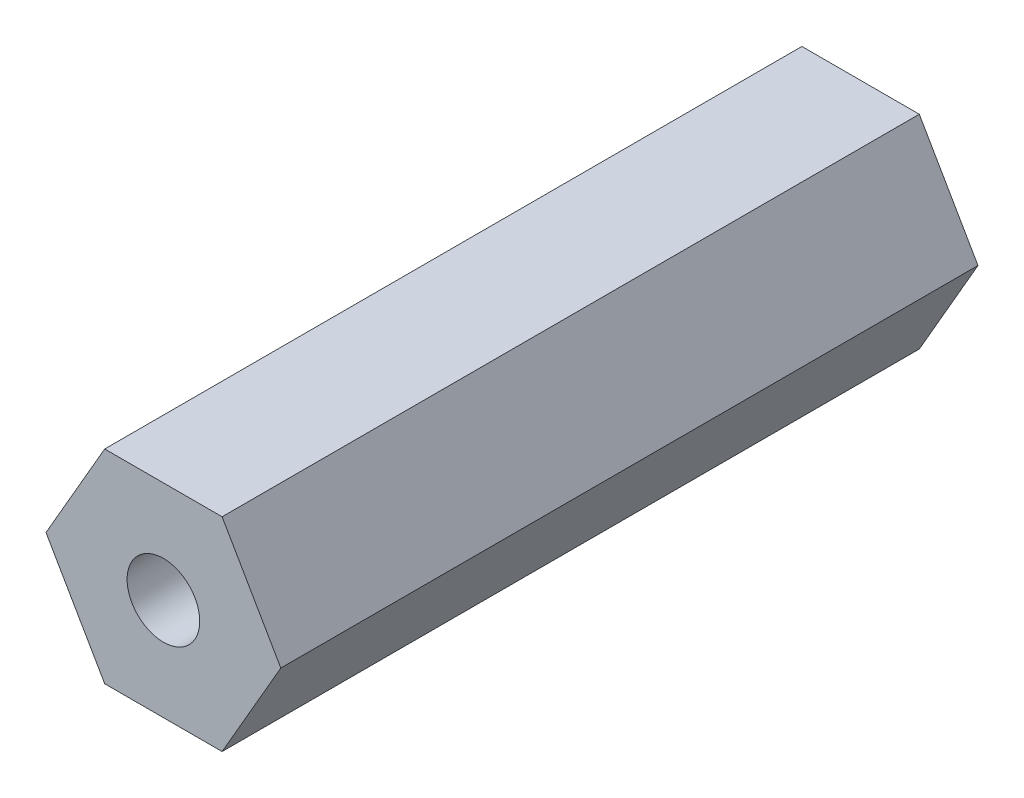
SolidWorks part; units mm, degrees
ref_plane "前视基准面" through (0, 0, 0) normal (0, 0, 1) x (1, 0, 0)
ref_plane "上视基准面" through (0, 0, 0) normal (0, 1, 0) x (1, 0, 0)
ref_plane "右视基准面" through (0, 0, 0) normal (1, 0, 0) x (0, 0, -1)
sketch "草图1" plane through (0, 0, 0) normal (0, 0, 1) x (1, 0, 0)
  line L1 (4.0415, 0) -> (2.0207, 3.5)
  line L2 (2.0207, 3.5) -> (-2.0207, 3.5)
  line L3 (-2.0207, 3.5) -> (-4.0415, 0)
  line L4 (-4.0415, 0) -> (-2.0207, -3.5)
  line L5 (-2.0207, -3.5) -> (2.0207, -3.5)
  line L6 (2.0207, -3.5) -> (4.0415, 0)
  circle A0 centre (0, 0) radius 3.5 construction
  dimension "D1" = 7
extrude "凸台-拉伸1" add sketch "草图1" along normal blind 24
sketch "草图2" plane through (0, 0, 24) normal (0, 0, 1) x (1, 0, 0)
  circle A0 centre (0, 0) radius 1.5
  dimension "D1" = 3
extrude "凸台-拉伸2" [suppressed] add sketch "草图2" along normal blind 6
cosmetic thread "装饰螺纹线1" [suppressed] parameters "D2"=2.459
hole_wizard "M3 螺纹孔1" positions "草图3" profile "草图4" tap size "M3" standard "ISO"
sketch "草图3" plane through (0, 0, 0) normal (0, 0, -1) x (-1, 0, 0)
  point P0 (0, 0)
cosmetic thread "孔螺蚊线1"
sketch "草图4" plane through (0, 0, 0) normal (1, 0, 0) x (0, 1, 0)
  line L0 (0, 0) -> (0, 4.6511)
  line L1 (0, 4.6511) -> (1.25, 3.9)
  line L2 (1.25, 3.9) -> (1.25, 0)
  line L5 (1.25, 0) -> (0, 0)
  line L10 (0, 4.6511) -> (-1.25, 3.9) construction
  line L11 (0, -6.35) -> (0, 107.95) construction
  dimension "螺纹孔钻头直径" = 2.5
  dimension "螺纹孔钻头深度" = 3.9
  dimension "导头角度" = 118
hole_wizard "M3 螺纹孔2" positions "草图5" profile "草图6" tap size "M3" standard "ISO"
sketch "草图5" plane through (0, 0, 24) normal (0, 0, 1) x (1, 0, 0)
  point P0 (0, 0)
sketch "草图6" plane through (0, 0, 24) normal (1, 0, 0) x (0, -1, 0)
  line L0 (0, 0) -> (0, 4.6511)
  line L1 (0, 4.6511) -> (1.25, 3.9)
  line L2 (1.25, 3.9) -> (1.25, 0)
  line L5 (1.25, 0) -> (0, 0)
  line L10 (0, 4.6511) -> (-1.25, 3.9) construction
  line L11 (0, -6.35) -> (0, 107.95) construction
  dimension "螺纹孔钻头直径" = 2.5
  dimension "螺纹孔钻头深度" = 3.9
  dimension "导头角度" = 118
cosmetic thread "孔螺蚊线2" parameters "D1"=2.4, "D2"=3
